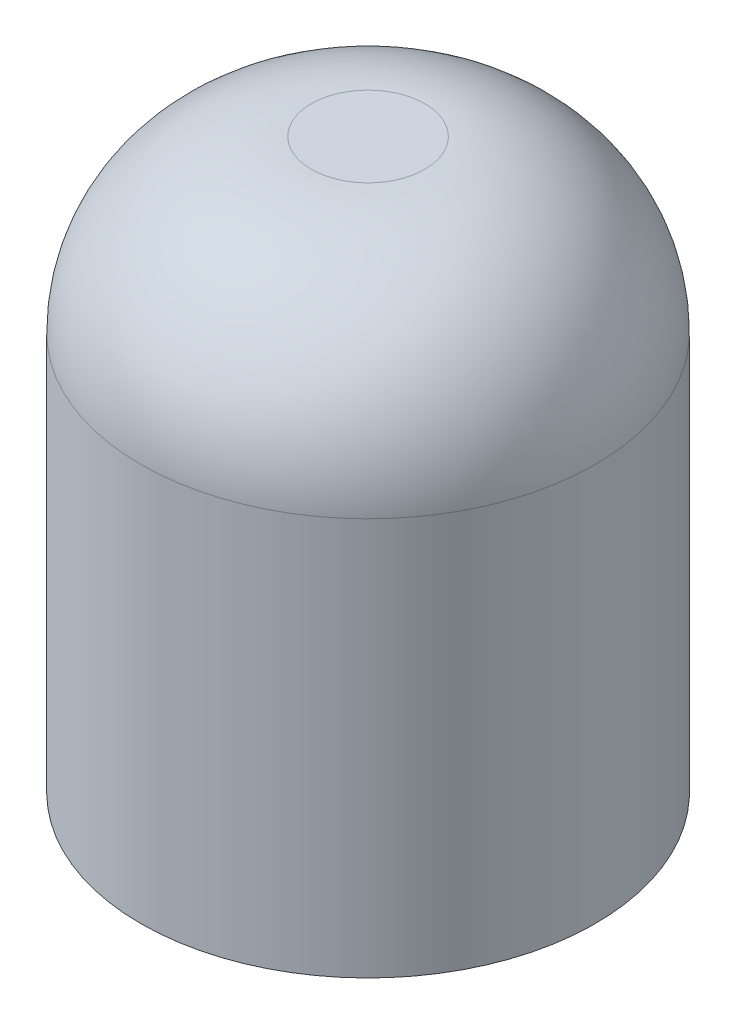
SolidWorks part; units mm, degrees
ref_plane "Front Plane" through (0, 0, 0) normal (0, 0, 1) x (1, 0, 0)
ref_plane "Top Plane" through (0, 0, 0) normal (0, 1, 0) x (1, 0, 0)
ref_plane "Right Plane" through (0, 0, 0) normal (1, 0, 0) x (0, 0, -1)
sketch "Sketch1" plane through (0, 0, 0) normal (0, 1, 0) x (1, 0, 0)
  circle A0 centre (0, 0) radius 4
  dimension "D1" = 8
extrude "Boss-Extrude1" add sketch "Sketch1" along normal blind 10
fillet "Fillet1" radius 3 1 edges at (0, 10, 4)
sketch "Sketch2" plane through (0, 0, 0) normal (0, -1, 0) x (1, 0, 0)
  circle A0 centre (0, 0) radius 1.5
  dimension "D1" = 3
extrude "Cut-Extrude1" cut sketch "Sketch2" against normal blind 5
